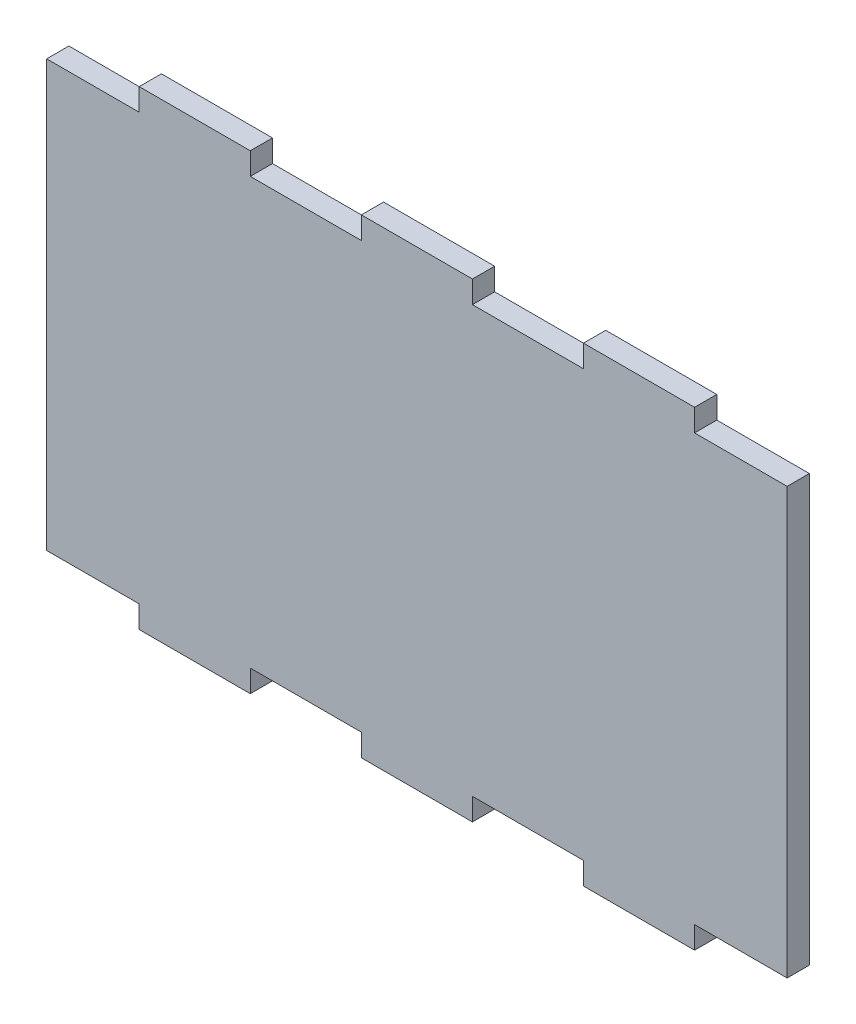
SolidWorks part; units mm, degrees
material "Acrylic (Medium-high impact)"
ref_plane "Ebene vorne" through (0, 0, 0) normal (0, 0, 1) x (1, 0, 0)
ref_plane "Ebene oben" through (0, 0, 0) normal (0, 1, 0) x (1, 0, 0)
ref_plane "Ebene rechts" through (0, 0, 0) normal (1, 0, 0) x (0, 0, -1)
sketch "Sketch1" plane through (0, 0, 0) normal (0, 0, 1) x (1, 0, 0)
  line L1 (50, -31.75) -> (-50, -31.75)
  line L2 (50, -31.75) -> (50, 31.75)
  line L3 (50, 31.75) -> (-50, 31.75)
  line L4 (-50, -31.75) -> (-50, 31.75)
  line L5 (50, -31.75) -> (-50, 31.75) construction
  line L6 (50, 31.75) -> (-50, -31.75) construction
  point P0 (0, 0)
  dimension "D1" = 100
  dimension "D2" = 63.5
extrude "Boss-Extrude1" add sketch "Sketch1" along normal blind 3
sketch "Sketch2" plane through (0, 0, 3) normal (0, 0, 1) x (1, 0, 0)
  line L1 (50, 31.75) -> (-50, 31.75) construction
  line L2 (-50, 31.75) -> (-37.5, 31.75)
  line L3 (-50, 31.75) -> (-50, 28.75)
  line L4 (-50, 28.75) -> (-37.5, 28.75)
  line L6 (-37.5, 31.75) -> (-37.5, 28.75)
  line L7 (-22.5, 28.75) -> (-7.5, 28.75)
  line L8 (-22.5, 28.75) -> (-22.5, 31.75)
  line L9 (-22.5, 31.75) -> (-7.5, 31.75)
  line L10 (-7.5, 28.75) -> (-7.5, 31.75)
  line L11 (-7.5, 31.75) -> (-7.5, 28.75) construction
  line L12 (22.5, 31.75) -> (22.5, 28.75) construction
  line L13 (7.5, 28.75) -> (22.5, 28.75)
  line L14 (7.5, 28.75) -> (7.5, 31.75)
  line L15 (7.5, 31.75) -> (22.5, 31.75)
  line L16 (22.5, 28.75) -> (22.5, 31.75)
  line L18 (37.5, 28.75) -> (50, 28.75)
  line L19 (37.5, 28.75) -> (37.5, 31.75)
  line L20 (37.5, 31.75) -> (50, 31.75)
  line L21 (50, 28.75) -> (50, 31.75)
  dimension "D1" = 12.5
  dimension "D2" = 3
  dimension "D3" = 3
  dimension "D4" = 3
  dimension "D5" = 15
  dimension "D6" = 12.5
extrude "Cut-Extrude1" cut sketch "Sketch2" against normal through all
mirror "Mirror2" about plane through (0, 0, 0) normal (0, 1, 0) of "Cut-Extrude1"
